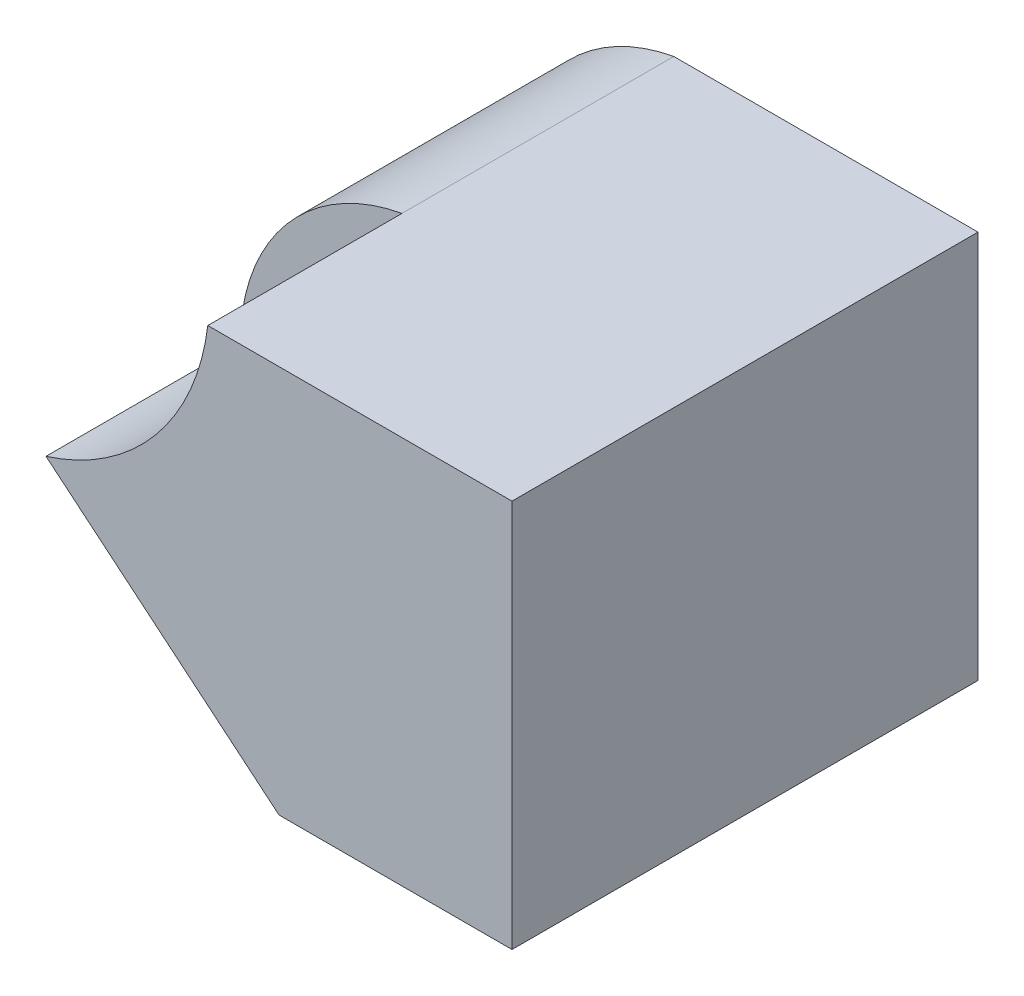
SolidWorks part; units mm, degrees
ref_plane "Front" through (0, 0, 0) normal (0, 0, 1) x (1, 0, 0)
ref_plane "Top" through (0, 0, 0) normal (0, 1, 0) x (1, 0, 0)
ref_plane "Right" through (0, 0, 0) normal (1, 0, 0) x (0, 0, -1)
sketch "Sketch1" plane through (0, 0, 0) normal (0, 1, 0) x (1, 0, 0)
  line L1 (-3, -3) -> (3, -3)
  line L2 (-3, -3) -> (-3, 3)
  line L3 (-3, 3) -> (3, 3)
  line L4 (3, -3) -> (3, 3)
  line L5 (-3, -3) -> (3, 3) construction
  line L6 (-3, 3) -> (3, -3) construction
  point P0 (0, 0)
  dimension "D1" = 6
  dimension "D2" = 6
extrude "Boss-Extrude1" add sketch "Sketch1" along normal blind 5
sketch "Sketch5" plane through (0, 0, 3) normal (0, 0, 1) x (1, 0, 0)
  line L0 (-3, 5) -> (3, 5) construction
  line L1 (-3, 0) -> (3, 0) construction
  line L2 (-3, 5) -> (-3, 0) construction
  line L7 (-3, 0) -> (3, 0)
  line L8 (3, 0) -> (3, 5)
  line L9 (3, 5) -> (-3, 5)
  line L10 (-3, 5) -> (-3, 0)
  line L11 (-3, 0) -> (3, 0)
  line L12 (3, 0) -> (3, 5)
  line L13 (3, 5) -> (-3, 5)
  line L14 (-3, 5) -> (-3, 0)
  arc A0 (0, 5) -> (0, 0) centre (-0.4583, 2.5) ccw
  point P9 (-1.5568, 5)
  point P10 (0, 0)
  point P11 (0, 0)
  point P13 (0, 5)
  line M5 (-3, 0) -> (3, 0)
  line M7 (3, 5) -> (-3, 5)
  line M8 (-3, 5) -> (-3, 0)
  dimension "D1" = 0
extrude "Cut-Extrude2" cut sketch "Sketch5" against normal blind 10 contours A0 M7 M8 | A0 L14 M5
sketch "Sketch6" plane through (0, 0, 3) normal (0, 0, 1) x (1, 0, 0)
  line L0 (-3, 2.5) -> (0, 0)
  line L4 (-0.9167, 0) -> (3, 0)
  line L5 (3, 0) -> (3, 5)
  line L6 (3, 5) -> (-0.9167, 5)
  line L7 (-0.9167, 0) -> (3, 0)
  line L8 (3, 0) -> (3, 5)
  line L9 (3, 5) -> (-0.9167, 5)
  arc A0 (-3, 2.5) -> (-0.9167, 5) centre (-3.8946, 5.3635) ccw
  arc A1 (-0.9167, 5) -> (-0.9167, 0) centre (-0.4583, 2.5) ccw construction
  arc A3 (-0.9167, 5) -> (-0.9167, 0) centre (-0.4583, 2.5) ccw
  arc A4 (-0.9167, 5) -> (-0.9167, 0) centre (-0.4583, 2.5) ccw
  arc M6 (-0.9167, 5) -> (-0.9167, 0) centre (-0.4583, 2.5) ccw
  line M7 (-0.9167, 0) -> (3, 0)
  dimension "D1" = 0
extrude "Cut-Extrude3" cut sketch "Sketch6" against normal blind 2.5 contours A0 M6 | L0 M6 M7
